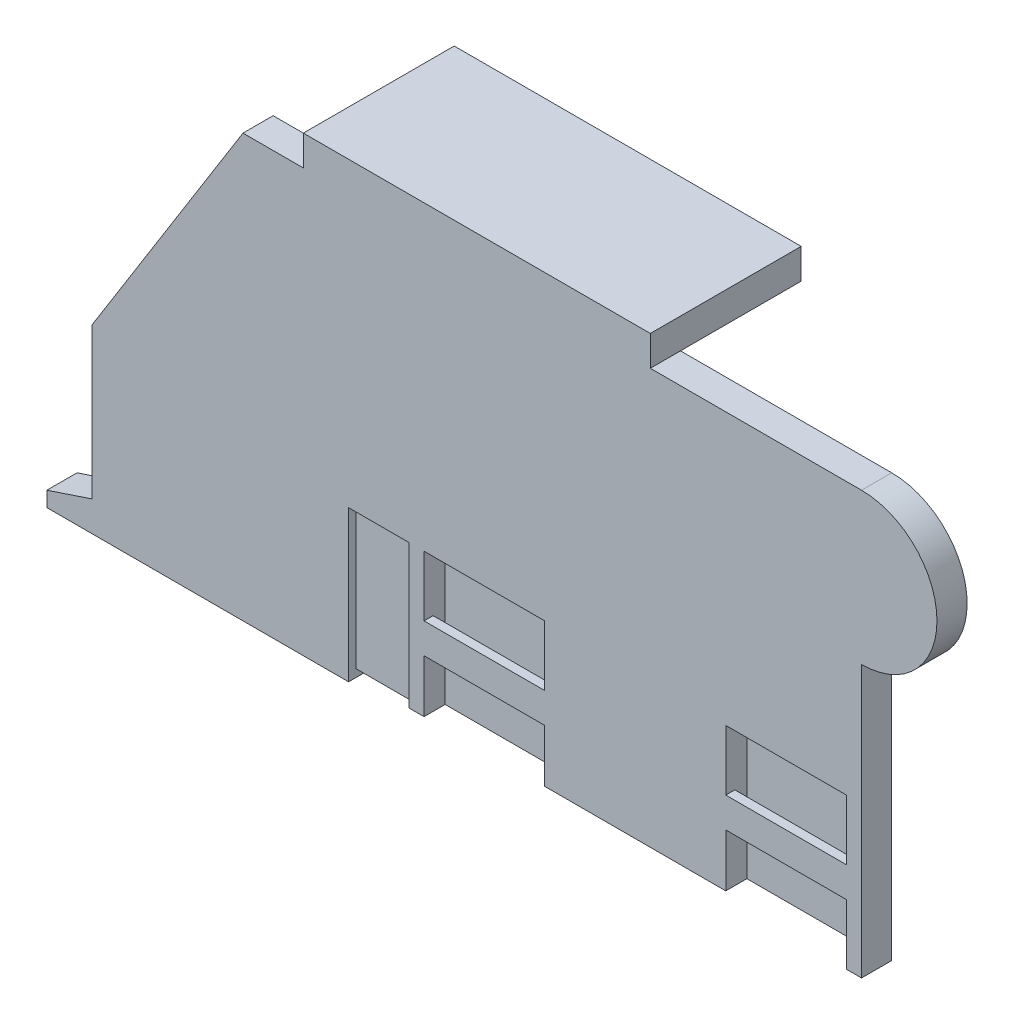
SolidWorks part; units mm, degrees
ref_plane "Front Plane" through (0, 0, 0) normal (0, 0, 1) x (1, 0, 0)
ref_plane "Top Plane" through (0, 0, 0) normal (0, 1, 0) x (1, 0, 0)
ref_plane "Right Plane" through (0, 0, 0) normal (1, 0, 0) x (0, 0, -1)
sketch "Sketch1" plane through (0, 0, 0) normal (0, 0, 1) x (1, 0, 0)
  line L0 (0, 0) -> (54, 0)
  line L1 (54, 0) -> (54, 18)
  line L2 (54, 28) -> (13, 28)
  line L3 (0, 0) -> (0, 1)
  line L4 (0, 1) -> (3, 2)
  line L5 (3, 2) -> (3, 12)
  line L6 (3, 12) -> (13, 28)
  arc A0 (54, 18) -> (54, 28) centre (54, 23) ccw
  point P9 (1.4395, 38.9108)
  point P10 (0, 0)
  point P12 (0, 0)
  point P13 (0, 0)
  point P14 (0, 0)
  dimension "D8" = 5
  dimension "D1" = 54
  dimension "D2" = 28
  dimension "D3" = 41
  dimension "D4" = 1
  dimension "D5" = 2
  dimension "D6" = 3
  dimension "D7" = 12
  dimension "D9" = 13
extrude "MainPlate" add sketch "Sketch1" against normal blind 2
sketch "TopPlate" plane through (0, 28, 0) normal (0, 1, 0) x (1, 0, 0)
  line L0 (54, 0) -> (13, 0) construction
  line L1 (17, 0) -> (40, 0)
  line L2 (17, 0) -> (17, 10)
  line L3 (17, 10) -> (40, 10)
  line L4 (40, 0) -> (40, 10)
  dimension "D1" = 10
  dimension "D2" = 23
  dimension "D3" = 4
extrude "Boss-Extrude6" add sketch "TopPlate" along normal blind 2
sketch "Sketch7" plane through (0, 0, 0) normal (0, -1, 0) x (1, 0, 0)
  line L0 (54, -2) -> (54, 0) construction
  line L1 (45, -0.6) -> (53, -0.6)
  line L2 (45, -0.6) -> (45, -1.4)
  line L3 (45, -1.4) -> (53, -1.4)
  line L4 (53, -0.6) -> (53, -1.4)
  line L5 (25, -0.6) -> (33, -0.6)
  line L6 (25, -0.6) -> (25, -1.4)
  line L7 (25, -1.4) -> (33, -1.4)
  line L8 (33, -0.6) -> (33, -1.4)
  line L9 (0, -2) -> (54, -2) construction
  line L10 (17, -2) -> (40, -2) construction
  dimension "D1" = 8
  dimension "D2" = 1
  dimension "D3" = 12
  dimension "D4" = 0.8
  dimension "D5" = 0.8
  dimension "D6" = 0.6
  dimension "D7" = 0.6
  dimension "D8" = 8
extrude "SlotsForMetalTabs" cut sketch "Sketch7" against normal blind 10
sketch "Sketch8" plane through (0, 0, 0) normal (0, 0, 1) x (1, 0, 0)
  line L0 (0, 0) -> (54, 0) construction
  line L5 (45, 10) -> (53, 10)
  line L6 (45, 10) -> (45, 6)
  line L7 (45, 6) -> (53, 6)
  line L8 (53, 10) -> (53, 6)
  line L9 (45, 0) -> (53, 0)
  line L10 (45, 0) -> (45, 4)
  line L11 (45, 4) -> (53, 4)
  line L12 (53, 0) -> (53, 4)
  line L13 (54, 0) -> (54, 18) construction
  line L15 (25, 0) -> (33, 0)
  line L16 (25, 0) -> (25, 4)
  line L17 (25, 4) -> (33, 4)
  line L18 (33, 0) -> (33, 4)
  line L19 (25, 10) -> (33, 10)
  line L20 (25, 10) -> (25, 6)
  line L21 (25, 6) -> (33, 6)
  line L22 (33, 10) -> (33, 6)
  dimension "D1" = 4
  dimension "D2" = 2
  dimension "D3" = 4
  dimension "D4" = 8
  dimension "D5" = 8
  dimension "D6" = 1
  dimension "D7" = 1
  dimension "D8" = 4
  dimension "D9" = 4
  dimension "D10" = 8
  dimension "D11" = 8
  dimension "D12" = 2
  dimension "D13" = 12
  dimension "D14" = 12
extrude "AccessHolesForMetalTabs" cut sketch "Sketch8" against normal blind 1
sketch "Sketch9" plane through (0, 0, 0) normal (0, 0, 1) x (1, 0, 0)
  line L0 (0, 0) -> (25, 0) construction
  line L1 (24, 0) -> (20, 0)
  line L2 (24, 0) -> (24, 10)
  line L3 (24, 10) -> (20, 10)
  line L4 (20, 0) -> (20, 10)
  dimension "D1" = 4
  dimension "D2" = 10
  dimension "D3" = 20
extrude "Cut-Extrude3" cut sketch "Sketch9" against normal blind 0.5
sketch "Sketch10" plane through (0, 0, 0) normal (0, 0, 1) x (1, 0, 0)
  line L0 (20, 10) -> (20, 0) construction
  line L1 (20, 0.5) -> (53, 0.5)
  line L2 (20, 0.5) -> (20, 0)
  line L3 (20, 0) -> (53, 0)
  line L4 (53, 0.5) -> (53, 0)
  dimension "D1" = 0.5
extrude "Cut-Extrude4" cut sketch "Sketch10" against normal through all
sketch "Sketch11" plane through (0, 0, 0) normal (0, 0, 1) x (1, 0, 0)
  line L0 (54, 18) -> (54, 28) construction
  line L1 (54, 28) -> (54, 23) construction
  line L2 (54, 23) -> (59, 23) construction
  line L3 (3, 10) -> (7, 10) construction
  line L4 (3, 12) -> (3, 2) construction
  line L5 (7, 0) -> (7, 10) construction
  line L6 (0, 0) -> (20, 0) construction
  line L7 (42, 0.5) -> (42, 3) construction
  line L8 (45, 0.5) -> (33, 0.5) construction
  line L9 (42, 3) -> (44.902, 3) construction
  line L10 (54, 0) -> (54, 18) construction
  arc A0 (54, 18) -> (54, 28) centre (54, 23) ccw construction
  circle A1 centre (7, 10) radius 2.5
  circle A2 centre (42, 3) radius 2
  circle A3 centre (54, 23) radius 2
  dimension "D5" = 5
  dimension "D6" = 4
  dimension "D7" = 4
  dimension "D1" = 10
  dimension "D2" = 4
  dimension "D3" = 2.5
  dimension "D4" = 12
  dimension "D8" = 20
  dimension "D9" = 7
  dimension "D10" = 35
  dimension "D11" = 47
